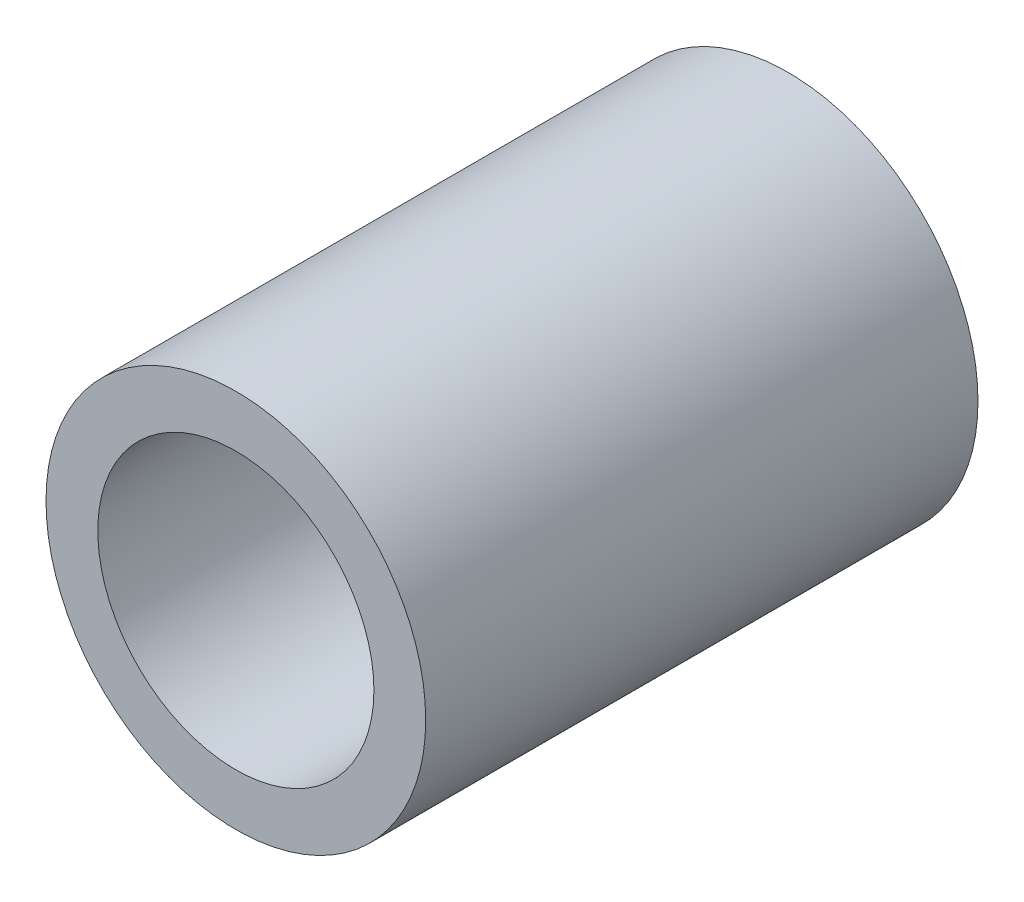
SolidWorks part; units mm, degrees
material "SMA"
ref_plane "Plano frontal" through (0, 0, 0) normal (0, 0, 1) x (1, 0, 0)
ref_plane "Plano superior" through (0, 0, 0) normal (0, 1, 0) x (1, 0, 0)
ref_plane "Plano direito" through (0, 0, 0) normal (1, 0, 0) x (0, 0, -1)
sketch "Esboço1" plane through (0, 0, 0) normal (0, 0, 1) x (1, 0, 0)
  circle A0 centre (0, 0) radius 2
  circle A1 centre (0, 0) radius 2.75
  dimension "D1" = 5.5
  dimension "D2" = 4
extrude "Ressalto-extrusão1" add sketch "Esboço1" along normal blind 8
